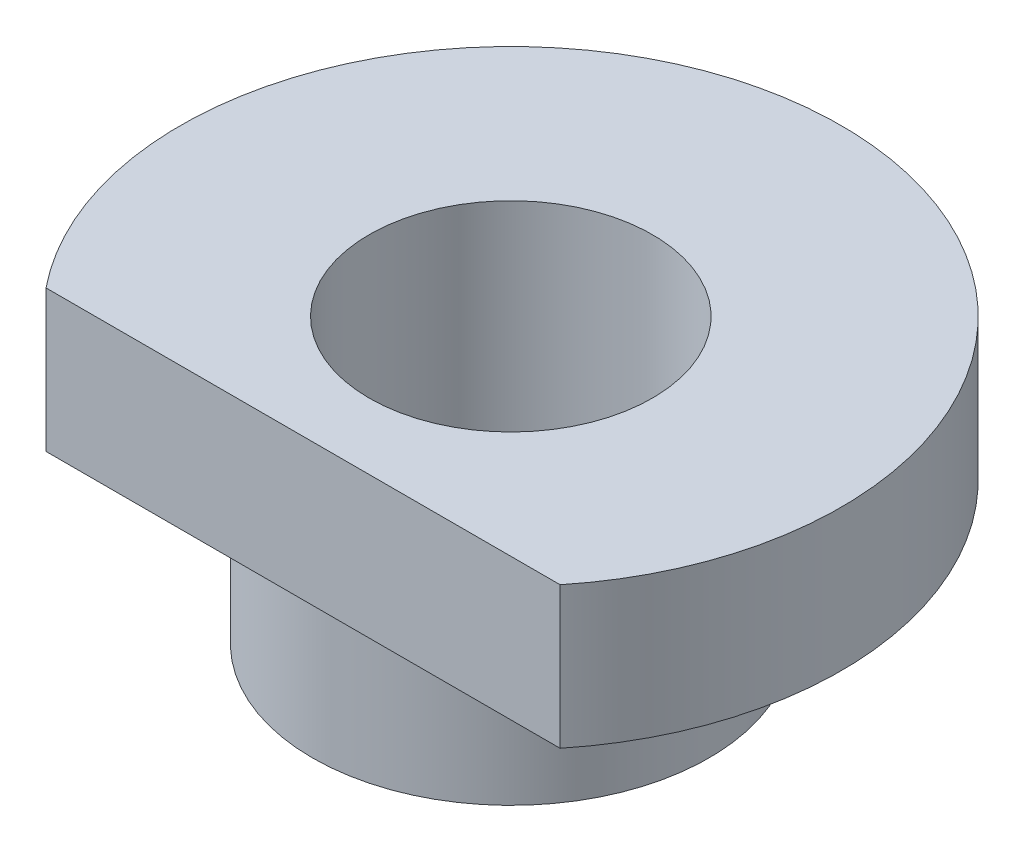
SolidWorks part; units mm, degrees
ref_plane "Plan de face" through (0, 0, 0) normal (0, 0, 1) x (1, 0, 0)
ref_plane "Plan de dessus" through (0, 0, 0) normal (0, 1, 0) x (1, 0, 0)
ref_plane "Plan de droite" through (0, 0, 0) normal (1, 0, 0) x (0, 0, -1)
sketch "Esquisse1" plane through (0, 0, 0) normal (0, 0, 1) x (1, 0, 0)
  line L0 (0, 0) -> (0, -25.7874) construction
  line L1 (0, -25.7874) -> (0, 0) construction
  line L2 (2.1, 0) -> (3.5, 0)
  line L3 (3.5, 0) -> (3.5, 1.5)
  line L4 (3.5, 1.5) -> (1.5, 1.5)
  line L5 (1.5, 1.5) -> (1.5, -1.5)
  line L6 (1.5, -1.5) -> (2.1, -1.5)
  line L7 (2.1, -1.5) -> (2.1, 0)
  dimension "D1" = 7
  dimension "D2" = 3
  dimension "D3" = 4.2
  dimension "D4" = 1.5
revolve "Révolution1" add sketch "Esquisse1" angle 360 about L0
sketch "Esquisse2" plane through (0, 0, 0) normal (0, 0, 1) x (1, 0, 0)
  line L1 (4.0302, -1.8037) -> (-4.0302, -1.8037)
  line L2 (4.0302, -1.8037) -> (4.0302, 1.8037)
  line L3 (4.0302, 1.8037) -> (-4.0302, 1.8037)
  line L4 (-4.0302, -1.8037) -> (-4.0302, 1.8037)
  line L5 (4.0302, -1.8037) -> (-4.0302, 1.8037) construction
  line L6 (4.0302, 1.8037) -> (-4.0302, -1.8037) construction
  point P0 (0, 0)
extrude "Enlèv. mat.-Extru.1" cut sketch "Esquisse2" along normal blind 10 from offset 2.2
